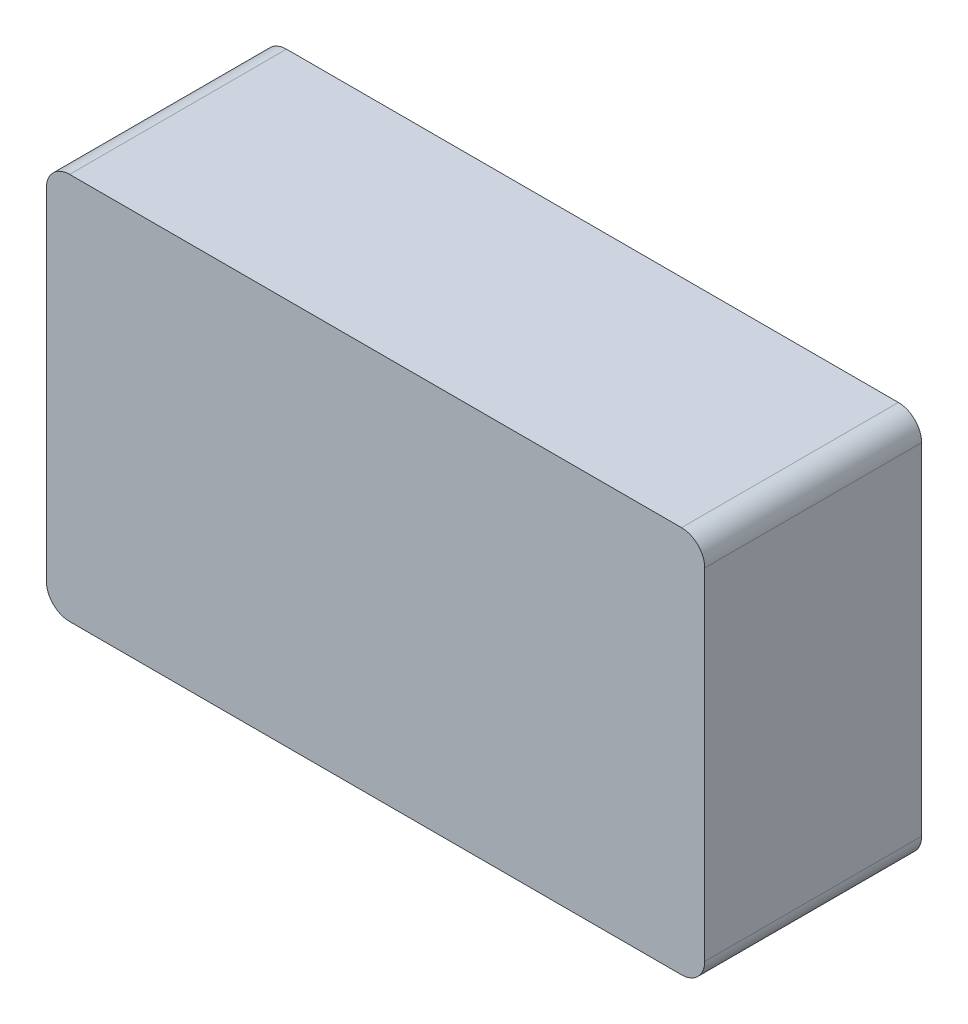
SolidWorks part; units mm, degrees
ref_plane "Plan de face" through (0, 0, 0) normal (0, 0, 1) x (1, 0, 0)
ref_plane "Plan de dessus" through (0, 0, 0) normal (0, 1, 0) x (1, 0, 0)
ref_plane "Plan de droite" through (0, 0, 0) normal (1, 0, 0) x (0, 0, -1)
sketch "Esquisse1" plane through (0, 0, 0) normal (0, 0, 1) x (1, 0, 0)
  line L1 (0, 0) -> (85, 0)
  line L2 (0, 0) -> (0, -50)
  line L3 (0, -50) -> (85, -50)
  line L4 (85, 0) -> (85, -50)
  dimension "D1" = 85
  dimension "D2" = 50
extrude "Boss.-Extru.1" add sketch "Esquisse1" along normal blind 28
fillet "Congé1" radius 3 4 edges at (0, -50, 14) (85, -50, 14) (85, 0, 14) (0, 0, 14)
